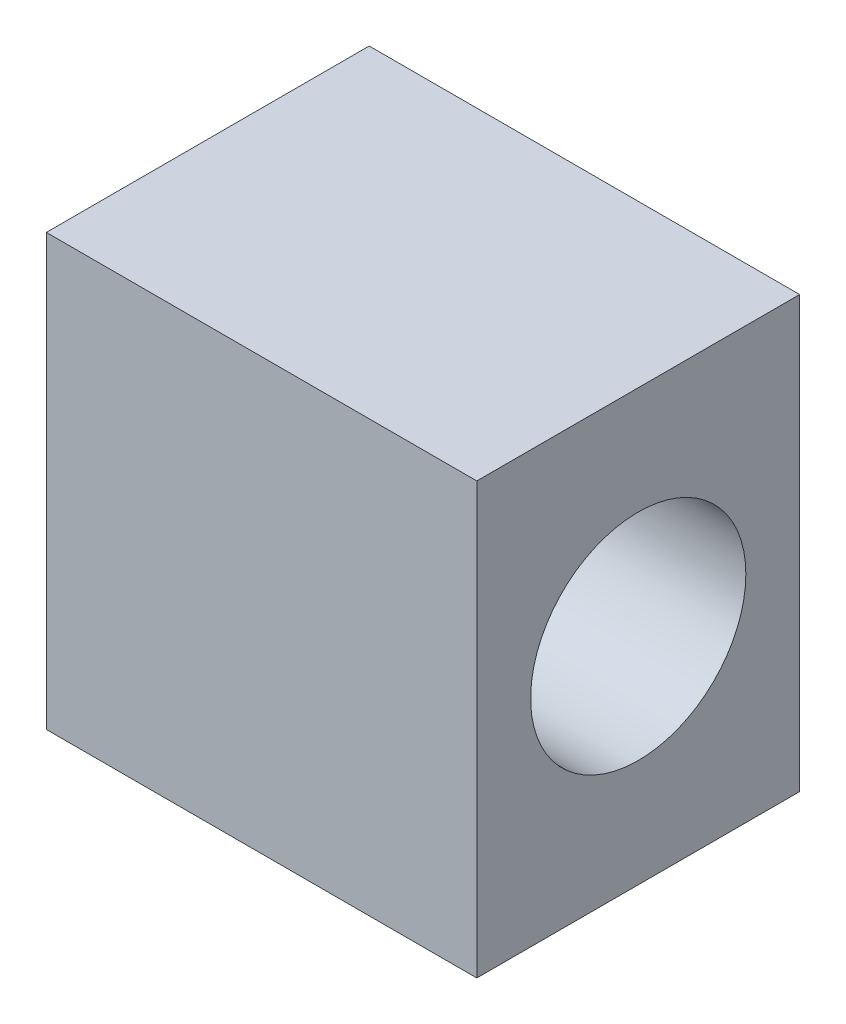
SolidWorks part; units mm, degrees
ref_plane "Front Plane" through (0, 0, 0) normal (0, 0, 1) x (1, 0, 0)
ref_plane "Top Plane" through (0, 0, 0) normal (0, 1, 0) x (1, 0, 0)
ref_plane "Right Plane" through (0, 0, 0) normal (1, 0, 0) x (0, 0, -1)
sketch "Sketch3" plane through (0, 0, 0) normal (0, 1, 0) x (1, 0, 0)
  line L0 (-10, 0) -> (10, 0) construction
  line L1 (0, 7.5) -> (0, -7.5) construction
  line L2 (-10, 7.5) -> (-10, -7.5)
  line L3 (-10, -7.5) -> (10, -7.5)
  line L4 (10, -7.5) -> (10, 7.5)
  line L5 (-10, 7.5) -> (10, 7.5)
  point P4 (0, 0)
  point P8 (0, 0)
  point P11 (-10, 0)
  point P16 (-10, 7.5)
  dimension "D1" = 15
  dimension "D2" = 20
extrude "Boss-Extrude1" add sketch "Sketch3" along normal blind 20
sketch "Sketch5" plane through (10, 0, 0) normal (1, 0, 0) x (0, 0, -1)
  circle A1 centre (0, 10) radius 5
extrude "Cut-Extrude1" cut sketch "Sketch5" against normal blind 10
sketch "Sketch6" plane through (-10, 0, 0) normal (-1, 0, 0) x (0, 0, 1)
  circle A0 centre (0, 10) radius 5
sketch "Sketch7" plane through (0, 0, 0) normal (0, -1, 0) x (1, 0, 0)
  circle A0 centre (0, 0) radius 5
